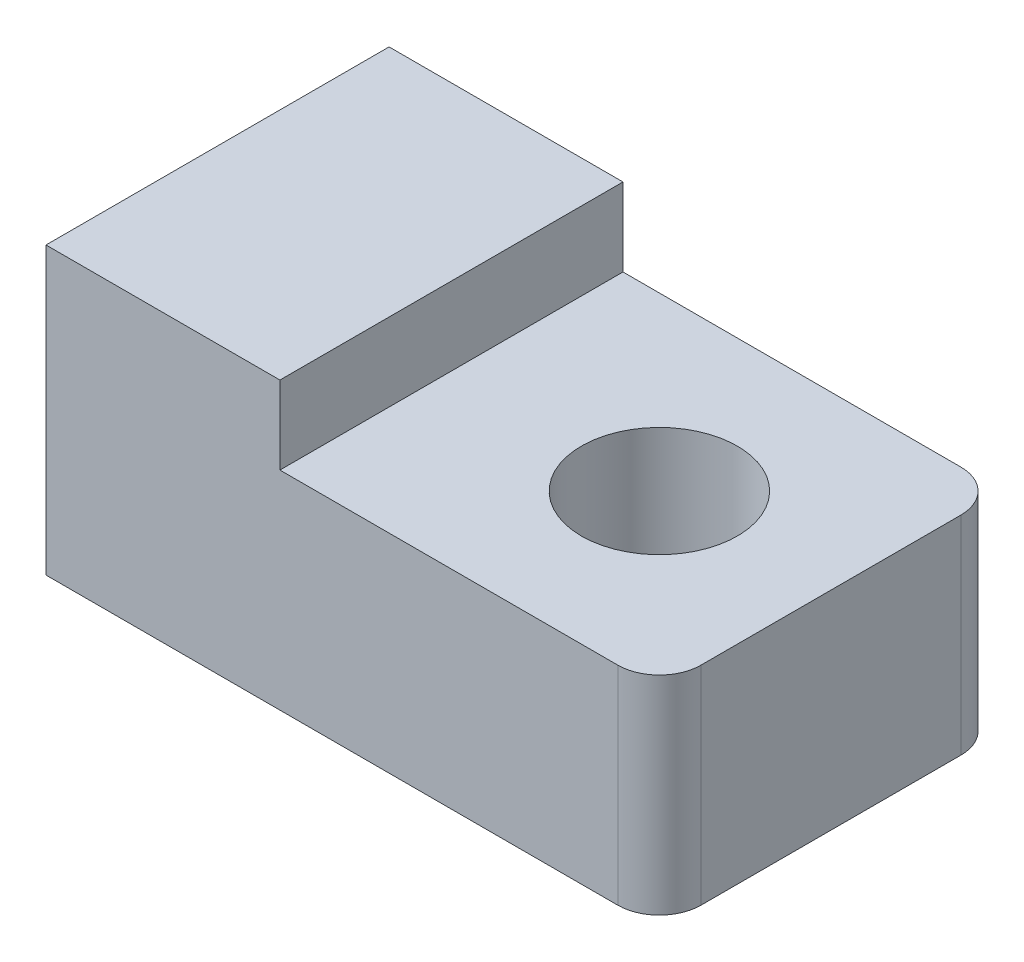
SolidWorks part; units mm, degrees
ref_plane "Front Plane" through (0, 0, 0) normal (0, 0, 1) x (1, 0, 0)
ref_plane "Top Plane" through (0, 0, 0) normal (0, 1, 0) x (1, 0, 0)
ref_plane "Right Plane" through (0, 0, 0) normal (1, 0, 0) x (0, 0, -1)
sketch "Sketch1" plane through (0, 0, 0) normal (0, 1, 0) x (1, 0, 0)
  line L0 (11.8, -1) -> (11.8, -6)
  line L5 (11, -0.2) -> (0, -0.2)
  line L6 (0, -0.2) -> (0, -6.8)
  line L7 (11, -6.8) -> (0, -6.8)
  arc A2 (11, -6.8) -> (11.8, -6) centre (11, -6) ccw
  arc A3 (11, -0.2) -> (11.8, -1) centre (11, -1) cw
  circle A4 centre (8.5, -3.5) radius 1.5
extrude "Boss-Extrude1" add sketch "Sketch1" along normal blind 4
sketch "Sketch2" plane through (0, 4, 0) normal (0, 1, 0) x (1, 0, 0)
  line L0 (0, -6.8) -> (11, -6.8) construction
  line L1 (0, -0.2) -> (4.5, -0.2)
  line L2 (0, -0.2) -> (0, -6.8)
  line L3 (0, -6.8) -> (4.5, -6.8)
  line L4 (4.5, -0.2) -> (4.5, -6.8)
extrude "Boss-Extrude2" add sketch "Sketch2" along normal blind 1.5
